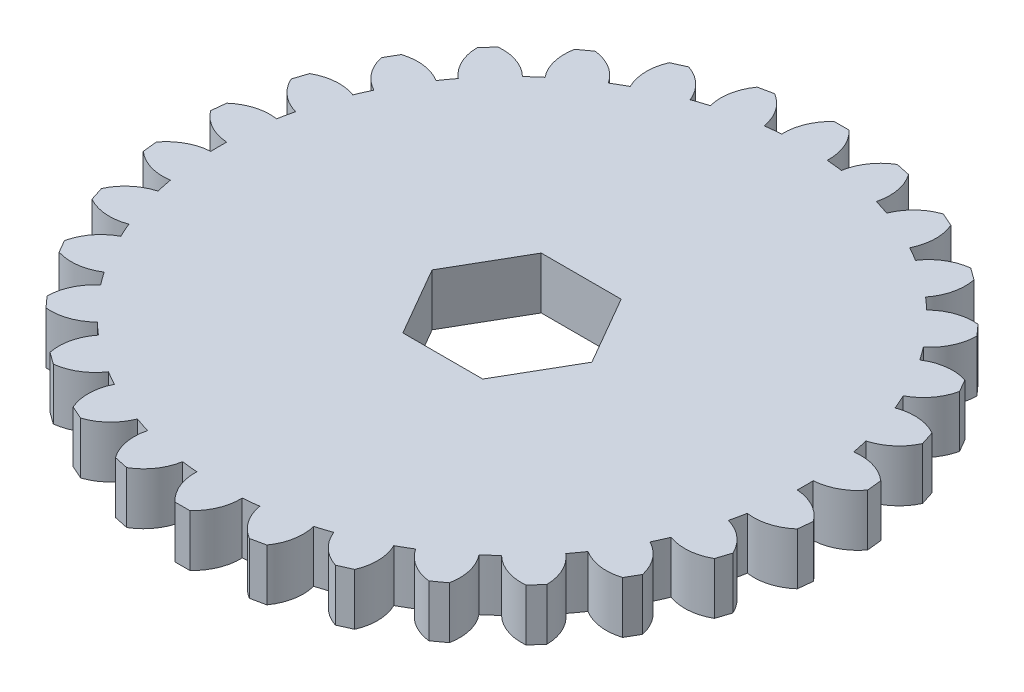
SolidWorks part; units mm, degrees
ref_plane "Front Plane" through (0, 0, 0) normal (0, 0, 1) x (1, 0, 0)
ref_plane "Top Plane" through (0, 0, 0) normal (0, 1, 0) x (1, 0, 0)
ref_plane "Right Plane" through (0, 0, 0) normal (1, 0, 0) x (0, 0, -1)
sketch "Sketch2" plane through (0, 0, 0) normal (0, 1, 0) x (1, 0, 0)
  line L1 (7.3323, 0) -> (3.6662, 6.35)
  line L2 (3.6662, 6.35) -> (-3.6662, 6.35)
  line L3 (-3.6662, 6.35) -> (-7.3323, 0)
  line L4 (-7.3323, 0) -> (-3.6662, -6.35)
  line L5 (-3.6662, -6.35) -> (3.6662, -6.35)
  line L6 (3.6662, -6.35) -> (7.3323, 0)
  circle A0 centre (0, 0) radius 26.9237
  circle A1 centre (0, 0) radius 6.35 construction
  dimension "D1" = 53.8474
  dimension "D2" = 12.7
  dimension "D3" = 6.35
extrude "Boss-Extrude2" add sketch "Sketch2" along normal blind 4.7625
sketch "Sketch1" plane through (0, 0, 0) normal (0, 1, 0) x (1, 0, 0)
  line L0 (0, 0) -> (-3.1793, 30.2495) construction
  line L1 (0, 0) -> (3.1793, 30.2495) construction
  line L2 (3.1793, 30.2495) -> (-3.1793, 30.2495) construction
  line L3 (-0.6733, 30.2495) -> (0.6733, 30.2495)
  line L4 (1.7564, 28.7026) -> (2.0843, 26.8429) construction
  line L5 (-1.7564, 28.7026) -> (-2.0843, 26.8429) construction
  line L6 (-1.7564, 28.7026) -> (-0.6733, 30.2495) construction
  line L7 (1.7564, 28.7026) -> (0.6733, 30.2495) construction
  line L8 (0, 30.2495) -> (0, 0) construction
  arc A1 (-2.8143, 26.7762) -> (2.0843, 26.8429) centre (0, 0) cw
  arc A2 (-0.6733, 30.2495) -> (-2.0843, 26.8429) centre (2.2739, 27.0332) ccw
  arc A3 (0.6733, 30.2495) -> (2.0843, 26.8429) centre (-2.2739, 27.0332) cw
  circle A4 centre (0, 0) radius 26.9237 construction
  circle A6 centre (0, 0) radius 26.9237 construction
  point P18 (-1.7564, 28.7026)
  dimension "D8" = 3.4924
  dimension "D9" = 53.8474
  dimension "D2" = 12
  dimension "D6" = 10
  dimension "D7" = 35
  dimension "D3" = 4.9058
  dimension "D4" = 2.55
  dimension "D5" = 1.56
extrude "Boss-Extrude3" add sketch "Sketch1" along normal blind 4.7625
pattern_circular "CirPattern1" count 30 over 360 about axis through (0, 0, 0) along (0, 1, 0) of "Boss-Extrude3"
